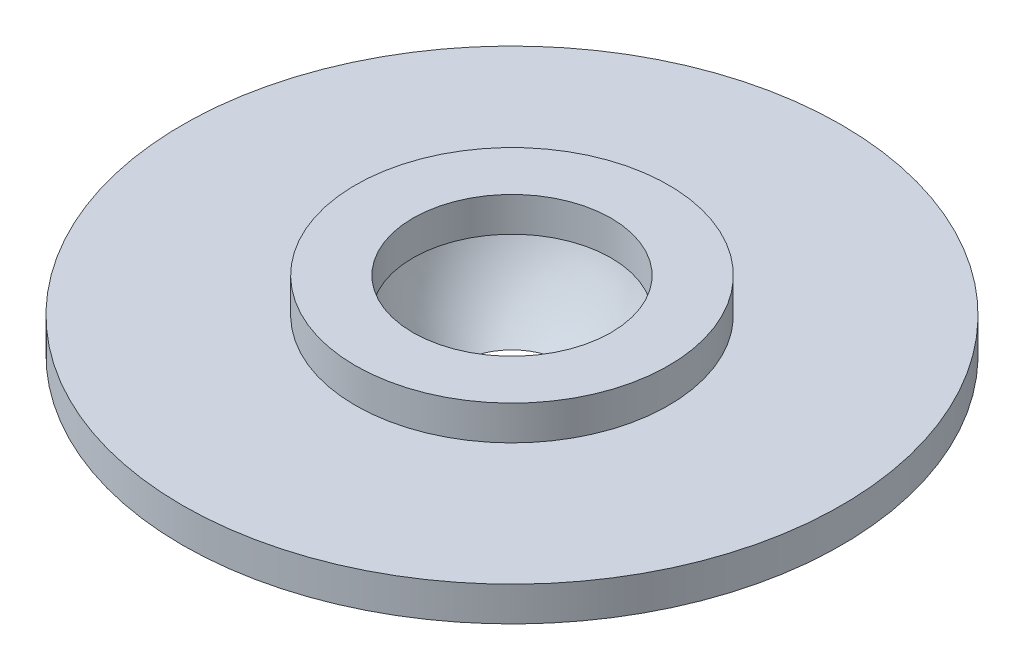
SolidWorks part; units mm, degrees
ref_plane "Спереди" through (0, 0, 0) normal (0, 0, 1) x (1, 0, 0)
ref_plane "Сверху" through (0, 0, 0) normal (0, 1, 0) x (1, 0, 0)
ref_plane "Справа" through (0, 0, 0) normal (1, 0, 0) x (0, 0, -1)
other "Configuration Table"
sketch "Эскиз1" plane through (0, 0, 0) normal (0, 0, 1) x (1, 0, 0)
  line L1 (12.03, 8.3612) -> (19, 8.3612)
  line L2 (19, 8.3612) -> (19, 4.1806)
  line L3 (19, 4.1806) -> (40, 4.1806)
  line L4 (40, 4.1806) -> (40, 0)
  line L5 (40, 0) -> (19, 0)
  line L6 (19, 0) -> (19, -4)
  line L7 (19, -4) -> (6.3989, -4)
  line L8 (12.03, 8.3612) -> (12.03, 4.1806)
  line L9 (0, 35.1514) -> (0, -27.4727) construction
  arc A1 (12.03, 4.1806) -> (6.3989, -4) centre (-7.9512, 11.9061) cw
revolve "Повернуть1" add sketch "Эскиз1" angle 360 about L9
